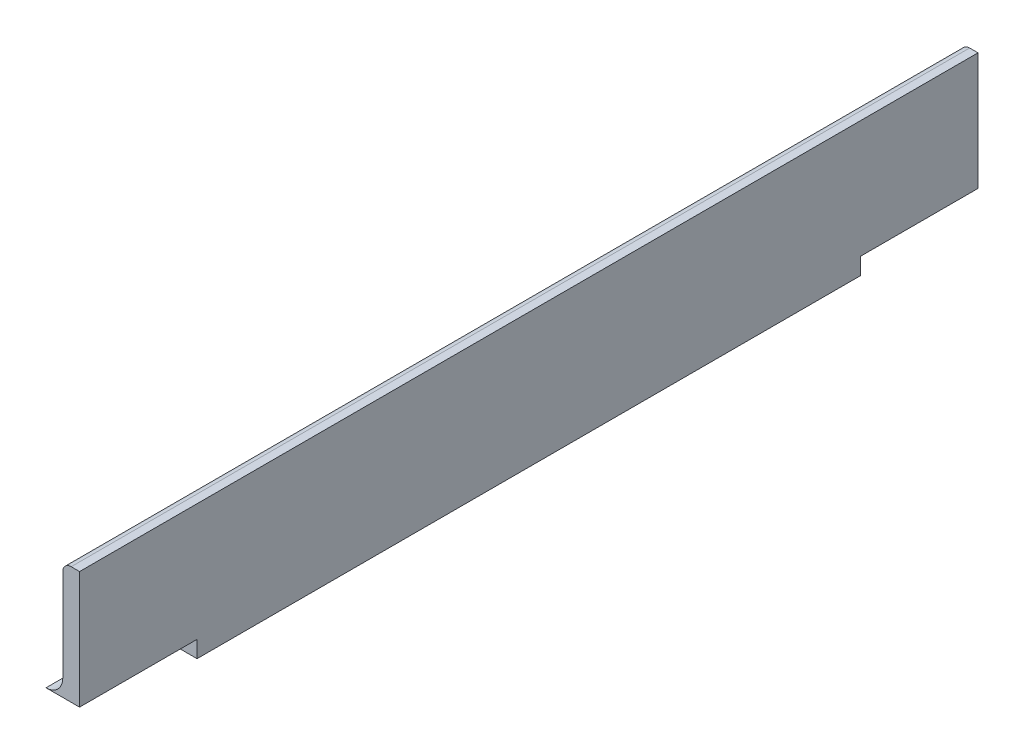
SolidWorks part; units mm, degrees
ref_plane "Front Plane" through (0, 0, 0) normal (0, 0, 1) x (1, 0, 0)
ref_plane "Top Plane" through (0, 0, 0) normal (0, 1, 0) x (1, 0, 0)
ref_plane "Right Plane" through (0, 0, 0) normal (1, 0, 0) x (0, 0, -1)
sketch "Sketch0" plane through (0, 0, 0) normal (0, 0, 1) x (1, 0, 0)
  line L0 (-12.7, -12.7) -> (12.7, -12.7)
  line L1 (12.7, -12.7) -> (12.7, 12.7)
  line L2 (12.7, 0) -> (0, 0) construction
  line L3 (0, 0) -> (0, -12.7) construction
  line L4 (9.525, -6.35) -> (9.525, 12.7) construction
  line L5 (6.35, -9.525) -> (-12.7, -9.525) construction
  arc A0 (9.525, -6.35) -> (6.35, -9.525) centre (6.35, -6.35) cw
  point P3 (8.5951, -8.5951)
  dimension "Inside Corner Radius" = 3.175
  dimension "Outside Height" = 25.4
  dimension "Inside Height" = 22.225
  dimension "Inside Width" = 22.225
  dimension "Wall Thickness" = 3.175
  dimension "D1" = 3.175
  dimension "Outside Width" = 25.4
sketch "Sketch1" plane through (0, 0, 0) normal (1, 0, 0) x (0, 0, -1)
  line L0 (609.6, 0) -> (-609.6, 0)
  point P4 (0, 0)
  dimension "Length" = 1219.2
sketch "Sketch2" plane through (0, 0, 0) normal (0, 0, 1) x (1, 0, 0)
  line L0 (-12.7, -12.7) -> (12.7, -12.7)
  line L1 (12.7, -12.7) -> (12.7, 12.7)
  line L2 (12.7, 12.7) -> (9.525, 12.7) construction
  line L3 (9.525, 11.1125) -> (9.525, -6.35)
  line L4 (6.35, -9.525) -> (-11.1125, -9.525)
  line L5 (-12.7, -12.7) -> (-12.7, -9.525) construction
  line L6 (11.1125, 12.7) -> (12.7, 12.7)
  line L7 (-12.7, -11.1125) -> (-12.7, -12.7)
  line L8 (12.7, 0) -> (0, 0) construction
  line L9 (0, 0) -> (0, -12.7) construction
  arc A0 (9.525, 11.1125) -> (11.1125, 12.7) centre (11.1125, 11.1125) cw
  arc A1 (-12.7, -11.1125) -> (-11.1125, -9.525) centre (-11.1125, -11.1125) cw
  arc A2 (9.525, -6.35) -> (6.35, -9.525) centre (6.35, -6.35) cw
  dimension "Inside Radius" = 3.175
  dimension "Height" = 25.4
  dimension "Width" = 25.4
  dimension "Thickness" = 3.175
extrude "Boss-Extrude1" add sketch "Sketch2" along normal mid plane 1219.2
sketch "Break Locations" plane through (0, 0, 0) normal (1, 0, 0) x (0, 0, -1)
  line L0 (-583.692, 0) -> (583.692, 0)
  line L1 (-609.6, -12.7) -> (-609.6, 12.7) construction
  line L2 (609.6, -12.7) -> (609.6, 12.7) construction
  point P0 (-588.01, 0)
  point P1 (588.01, 0)
  point P10 (0, 0)
  point P11 (583.692, 0)
  point P13 (-583.692, 0)
  dimension "D1" = 21.59
  dimension "D2" = 21.59
  dimension "D3" = 25.908
sketch "Sketch3" plane through (12.7, 0, 0) normal (1, 0, 0) x (0, 0, -1)
  line L0 (-609.6, -12.7) -> (609.6, -12.7) construction
  line L1 (609.6, 12.7) -> (-439.6, 12.7)
  line L2 (609.6, 12.7) -> (609.6, -12.7)
  line L3 (609.6, -12.7) -> (-439.6, -12.7)
  line L4 (-439.6, 12.7) -> (-439.6, -12.7)
  line L5 (-609.6, -12.7) -> (-609.6, 12.7) construction
  dimension "D1" = 170
extrude "Cut-Extrude2" cut sketch "Sketch3" against normal blind 30.48
sketch "Sketch4" plane through (0, -12.7, 0) normal (0, -1, 0) x (1, 0, 0)
  line L0 (-12.7, 609.6) -> (-12.7, 439.6) construction
  line L1 (-12.7, 471.825) -> (12.7, 471.825)
  line L2 (-12.7, 471.825) -> (-12.7, 439.6)
  line L3 (-12.7, 439.6) -> (12.7, 439.6)
  line L4 (12.7, 471.825) -> (12.7, 439.6)
  line L5 (-571.3, 471.825) -> (12.7, 471.825) construction
sketch "Sketch5" plane through (9.525, 0, 0) normal (-1, 0, 0) x (0, 0, 1)
  line L0 (524.6, 11.1125) -> (524.6, -12.7) construction
  line L1 (609.6, 11.1125) -> (439.6, 11.1125) construction
  line L2 (609.6, -12.7) -> (439.6, -12.7) construction
ref_plane "Plane1" through (0, 0, 529.6) normal (0, 0, 1) x (1, 0, 0)
sketch "Sketch6" plane through (0, 0, 439.6) normal (0, 0, -1) x (-1, 0, 0)
  line L0 (-6.35, -9.525) -> (11.1125, -9.525) construction
  line L1 (-12.7, -12.7) -> (12.7, -12.7)
  line L2 (-12.7, -12.7) -> (-12.7, -9.525)
  line L3 (-12.7, -9.525) -> (12.7, -9.525)
  line L4 (12.7, -12.7) -> (12.7, -9.525)
  line L5 (12.7, -11.1125) -> (12.7, -12.7) construction
extrude "Cut-Extrude4" cut sketch "Sketch6" against normal blind 22.23
sketch "Sketch7" plane through (0, 0, 609.6) normal (0, 0, 1) x (1, 0, 0)
  line L0 (6.35, -9.525) -> (-11.1125, -9.525) construction
  line L1 (12.7, -12.7) -> (-12.7, -12.7)
  line L2 (12.7, -12.7) -> (12.7, -9.525)
  line L3 (12.7, -9.525) -> (-12.7, -9.525)
  line L4 (-12.7, -12.7) -> (-12.7, -9.525)
  line L5 (-12.7, -11.1125) -> (-12.7, -12.7) construction
extrude "Cut-Extrude5" cut sketch "Sketch7" against normal blind 22.23
equation "\"D1@Break Locations\" = .85 * \"Height@Sketch2\""
equation "\"D2@Break Locations\"=\"D1@Break Locations\""
equation "\"Thickness@Sketch2\" = \"Wall Thickness@Sketch0\""
equation "\"Height@Sketch2\" = \"Outside Height@Sketch0\""
equation "\"Width@Sketch2\" = \"Outside Width@Sketch0\""
equation "\"Inside Radius@Sketch2\" = \"Inside Corner Radius@Sketch0\""
equation "\"Length@Boss-Extrude1\" = \"Length@Sketch1\""
equation "\"D3@Break Locations\"=\"D2@Break Locations\"*1.2"
equation "\"D1@Sketch0\"=\"Wall Thickness@Sketch0\""
